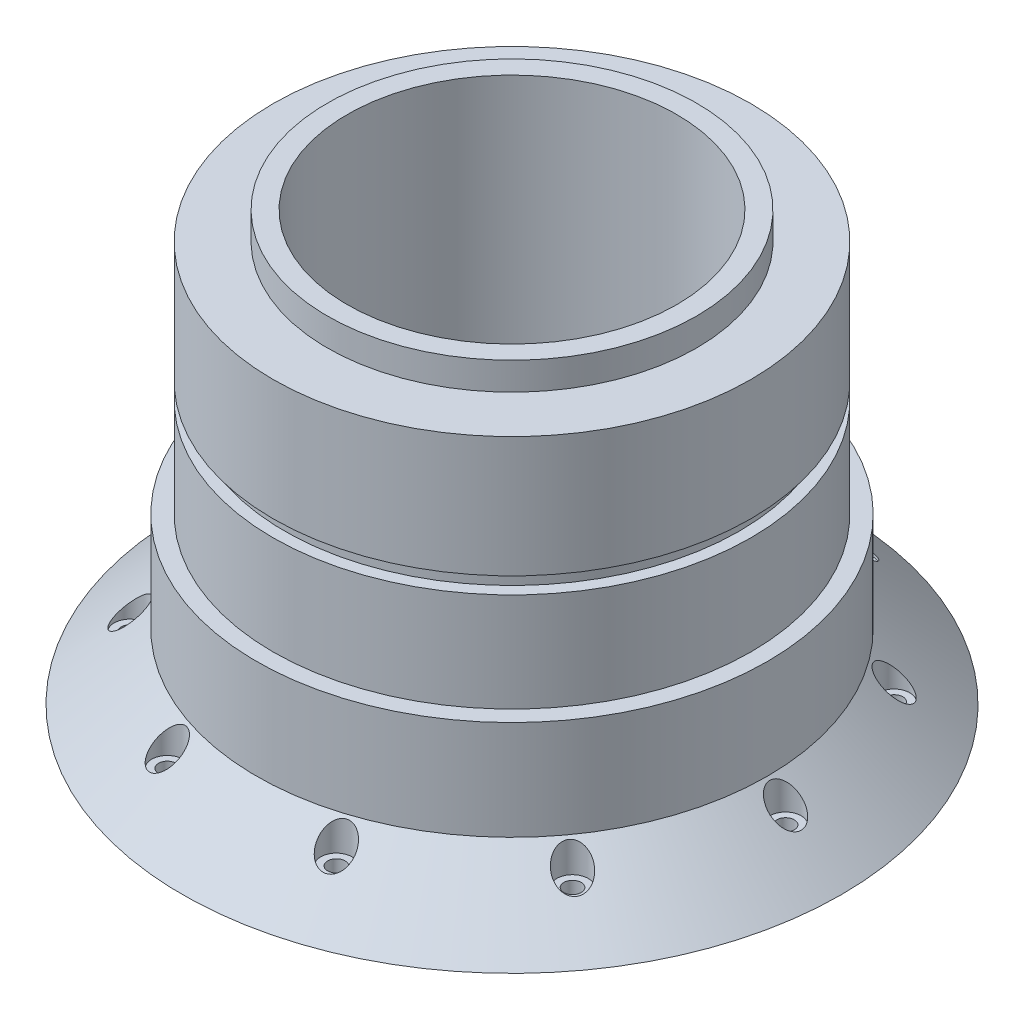
SolidWorks part; units mm, degrees
ref_plane "정면" through (0, 0, 0) normal (0, 0, 1) x (1, 0, 0)
ref_plane "윗면" through (0, 0, 0) normal (0, 1, 0) x (1, 0, 0)
ref_plane "우측면" through (0, 0, 0) normal (1, 0, 0) x (0, 0, -1)
sketch "스케치1" plane through (0, 0, 0) normal (0, 0, 1) x (1, 0, 0)
  line L0 (0, 0) -> (0, 35.8798)
  line L2 (-49.992, 36.7744) -> (-99.992, 36.7744)
  line L11 (-55.992, 158.3744) -> (-55.992, 166.7744)
  line L13 (-55.992, 166.7744) -> (-49.992, 166.7744)
  line L14 (-49.992, 166.7744) -> (-49.992, 36.7744)
  line L16 (-55.992, 158.3744) -> (-72.492, 158.3744)
  line L17 (-72.492, 158.3744) -> (-72.492, 121.7744)
  line L18 (-72.492, 121.7744) -> (-68.992, 121.7744)
  line L19 (-68.992, 121.7744) -> (-68.992, 116.7744)
  line L20 (-68.992, 116.7744) -> (-72.492, 116.7744)
  line L21 (-72.492, 116.7744) -> (-72.492, 86.7744)
  line L22 (-72.492, 86.7744) -> (-77.4909, 86.7744)
  line L23 (-77.4909, 86.7744) -> (-77.4909, 69.1692)
  line L24 (-77.4909, 69.1692) -> (-77.4909, 56.6163)
  line L26 (-77.4909, 56.6163) -> (-99.992, 36.7744)
  dimension "D2" = 50
  dimension "D3" = 50
  dimension "D4" = 30
  dimension "D5" = 50
  dimension "D6" = 80
  dimension "D7" = 4.9989
  dimension "D8" = 16.5
  dimension "D9" = 3.5
  dimension "D10" = 8.4
  dimension "D11" = 3.5
  dimension "D12" = 6
  dimension "D13" = 30
  dimension "D14" = 5
  dimension "D15" = 30.1581
revolve "회전1" add sketch "스케치1" angle 360 about L0
ref_plane "평면3" through (0, 56.6163, 0) normal (0, -1, 0) x (-1, 0, 0)
sketch "스케치74" plane through (0, 56.6163, 0) normal (0, -1, 0) x (-1, 0, 0)
  circle A0 centre (0, 0) radius 83
  point P3 (83, 0)
  point P7 (67.1484, -48.7862)
  point P8 (25.6484, -78.9377)
  point P9 (-25.6484, -78.9377)
  point P10 (-67.1484, -48.7862)
  point P11 (-83, 0)
  point P12 (-67.1484, 48.7862)
  point P13 (-25.6484, 78.9377)
  point P14 (25.6484, 78.9377)
  point P15 (67.1484, 48.7862)
  point P16 (0, 0)
  dimension "D1" = 10
hole_wizard "M5 치즈머리 홈붙이 머리용 카운터보어4" positions "스케치79" profile "스케치80" counterbore size "M5" standard "KS" end condition through all
sketch "스케치79" plane through (0, 56.6163, 0) normal (0, -1, 0) x (-1, 0, 0)
  point P0 (-83, 0)
  point P3 (-67.1484, 48.7862)
  point P6 (-25.6484, 78.9377)
  point P9 (25.6484, 78.9377)
  point P12 (67.1484, 48.7862)
  point P15 (83, 0)
  point P18 (67.1484, -48.7862)
  point P21 (-67.1484, -48.7862)
  point P24 (-25.6484, -78.9377)
  point P27 (25.6484, -78.9377)
sketch "스케치80" plane through (83, 56.6163, 0) normal (1, 0, 0) x (0, 0, 1)
  line L0 (0, 0) -> (0, 19.8419)
  line L1 (0, 19.8419) -> (2.65, 19.8419)
  line L3 (2.65, 19.8419) -> (2.65, 10)
  line L4 (2.65, 10) -> (4.75, 10)
  line L5 (4.75, 10) -> (4.75, 0)
  line L7 (4.75, 0) -> (0, 0)
  line L11 (0, -6.35) -> (0, 107.95) construction
  dimension "관통 구멍 지름" = 5.3
  dimension "관통 구멍 깊이" = 19.8419
  dimension "카운터보어 지름" = 9.5
  dimension "카운터보어 깊이" = 10
sketch "스케치81" plane through (0, 36.7744, 0) normal (0, -1, 0) x (1, 0, 0)
sketch "스케치82" plane through (0, 56.6163, 0) normal (0, -1, 0) x (-1, 0, 0)
